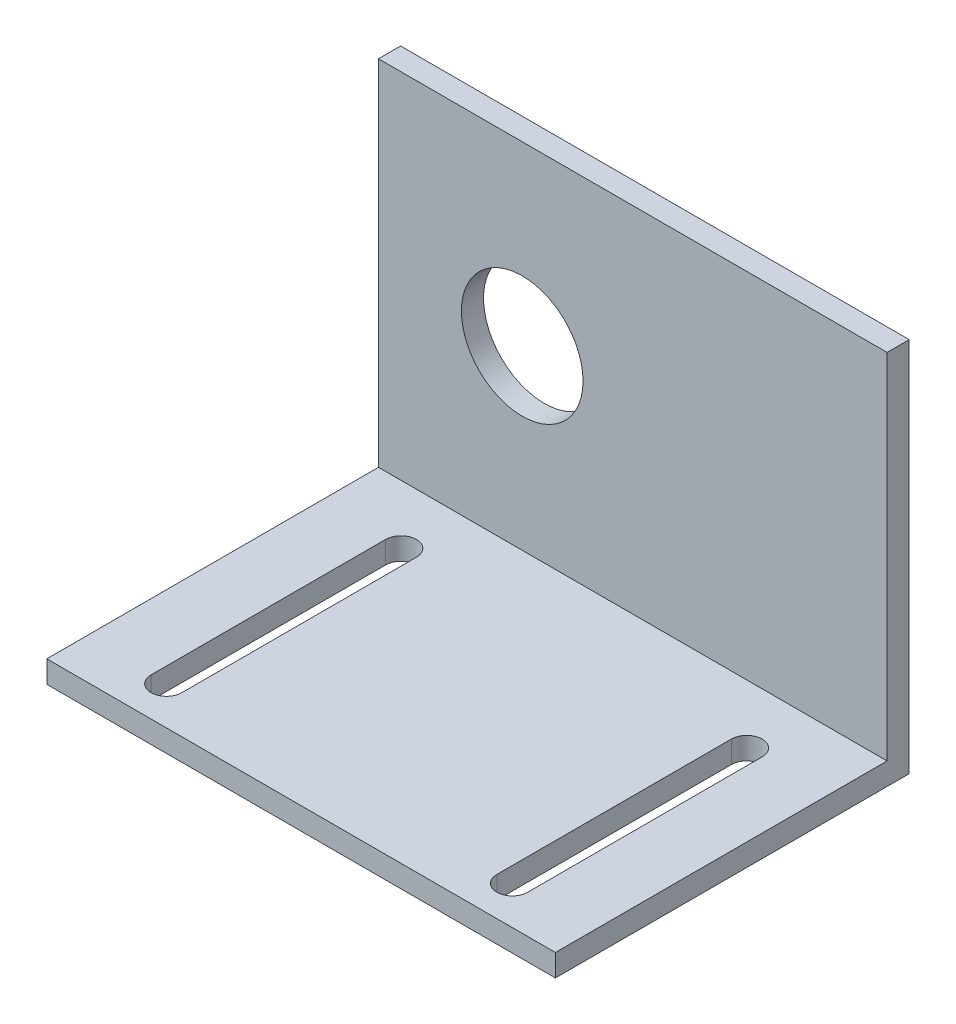
SolidWorks part; units mm, degrees
ref_plane "前视基准面" through (0, 0, 0) normal (0, 0, 1) x (1, 0, 0)
ref_plane "上视基准面" through (0, 0, 0) normal (0, 1, 0) x (1, 0, 0)
ref_plane "右视基准面" through (0, 0, 0) normal (1, 0, 0) x (0, 0, -1)
sketch "草图1" plane through (0, 0, 0) normal (0, 0, 1) x (1, 0, 0)
  line L0 (-30.2063, 34) -> (-30.2063, 0)
  line L1 (-30.2063, 0) -> (15.7937, 0)
  line L2 (15.7937, 0) -> (15.7937, 34)
  line L3 (15.7937, 34) -> (-30.2063, 34)
  dimension "D1" = 34
  dimension "D2" = 46
extrude "凸台-拉伸1" add sketch "草图1" along normal blind 2
sketch "草图2" plane through (0, 0, 2) normal (0, 0, 1) x (1, 0, 0)
  line L0 (-30.2063, 0) -> (-30.2063, 2)
  line L1 (-30.2063, 34) -> (-30.2063, 0) construction
  line L2 (-30.2063, 2) -> (15.7937, 2)
  line L3 (15.7937, 0) -> (15.7937, 34) construction
  line L4 (15.7937, 2) -> (15.7937, 0)
  line L5 (15.7937, 0) -> (-30.2063, 0)
  dimension "D1" = 2
extrude "凸台-拉伸2" add sketch "草图2" along normal blind 30
sketch "草图3" plane through (0, 0, 2) normal (0, 0, 1) x (1, 0, 0)
  line L0 (-30.2063, 34) -> (-30.2063, 18) construction
  line L2 (-30.2063, 34) -> (-30.2063, 2) construction
  line L3 (-30.2063, 18) -> (-17.2063, 18) construction
  circle A0 centre (-17.2063, 18) radius 5.5
  dimension "D3" = 11
  dimension "D1" = 16
  dimension "D2" = 13
extrude "切除-拉伸1" cut sketch "草图3" against normal blind 2
sketch "草图4" plane through (0, 2, 0) normal (0, 1, 0) x (1, 0, 0)
  line L0 (-7.2063, -2) -> (-7.2063, -32) construction
  line L2 (-24.2357, -7.3283) -> (-24.2357, -28.54)
  line L4 (-21.4476, -7.3283) -> (-21.4476, -28.54)
  line L5 (15.7937, -2) -> (-30.2063, -2) construction
  line L6 (15.7937, -32) -> (-30.2063, -32) construction
  line L7 (7.035, -7.3283) -> (7.035, -28.54)
  line L8 (9.8231, -7.3283) -> (9.8231, -28.54)
  arc A0 (-21.4476, -7.3283) -> (-24.2357, -7.3283) centre (-22.8416, -7.3283) ccw
  arc A1 (-24.2357, -28.54) -> (-21.4476, -28.54) centre (-22.8416, -28.54) ccw
  arc A2 (9.8231, -28.54) -> (7.035, -28.54) centre (8.4291, -28.54) cw
  arc A3 (7.035, -7.3283) -> (9.8231, -7.3283) centre (8.4291, -7.3283) cw
extrude "切除-拉伸2" cut sketch "草图4" against normal blind 2
